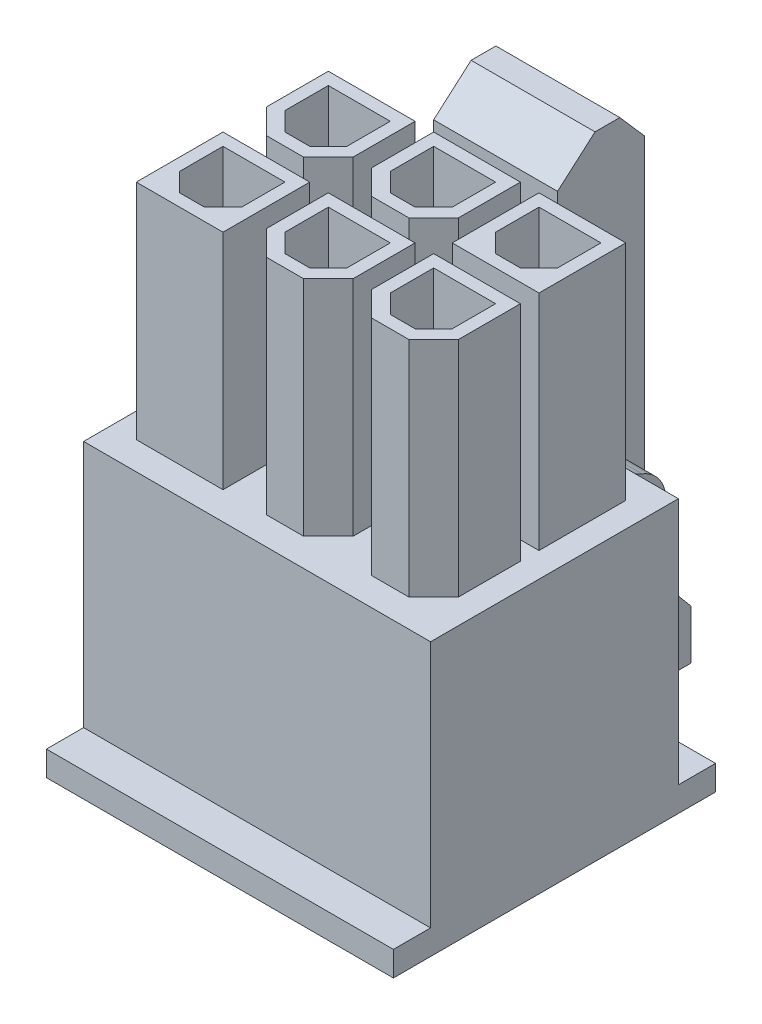
SolidWorks part; units mm, degrees
ref_plane "Ebene vorne" through (0, 0, 0) normal (0, 0, 1) x (1, 0, 0)
ref_plane "Ebene oben" through (0, 0, 0) normal (0, 1, 0) x (1, 0, 0)
ref_plane "Ebene rechts" through (0, 0, 0) normal (1, 0, 0) x (0, 0, -1)
sketch "Skizze1" plane through (0, 0, 0) normal (1, 0, 0) x (0, 0, -1)
  line L1 (5, 0) -> (-5, 0)
  line L2 (5, 0) -> (5, 11)
  line L3 (5, 11) -> (-5, 11)
  line L4 (-5, 0) -> (-5, 11)
  point P4 (0, 0)
  dimension "D1" = 10
  dimension "D2" = 11
extrude "Aufsatz-Linear austragen1" add sketch "Skizze1" along normal mid plane 14
sketch "Skizze2" plane through (0, 0, 0) normal (1, 0, 0) x (0, 0, -1)
  line L0 (0, 0) -> (0, 11) construction
  line L1 (-5, 0) -> (-6.5, 0)
  line L2 (-5, 0) -> (-5, 1)
  line L3 (-5, 1) -> (-6.5, 1)
  line L4 (-6.5, 0) -> (-6.5, 1)
  line L5 (5, 11) -> (-5, 11) construction
  line L6 (6.5, 0) -> (6.5, 1)
  line L7 (5, 1) -> (6.5, 1)
  line L8 (5, 0) -> (5, 1)
  line L9 (5, 0) -> (6.5, 0)
  dimension "D1" = 1.5
  dimension "D2" = 1
extrude "Aufsatz-Linear austragen2" add sketch "Skizze2" along normal mid plane 14
sketch "Skizze3" plane through (0, 0, 0) normal (1, 0, 0) x (0, 0, -1)
  line L0 (5, 11) -> (5.5717, 11)
  line L1 (7.5, 8.198) -> (7.5, 5.198)
  line L2 (7.5, 5.198) -> (8.5, 4)
  line L3 (8.5, 4) -> (8.5, 2)
  line L4 (8.5, 2) -> (6.5, 2)
  line L5 (6.5, 2) -> (6.5, 8)
  line L6 (6.5, 8) -> (5, 8)
  line L7 (5, 1) -> (5, 11) construction
  line L8 (5, 11) -> (5, 8)
  line L9 (-6.5, 0) -> (6.5, 0) construction
  arc A0 (5.5717, 11) -> (6.5359, 9.599) centre (7.0717, 11) ccw
  arc A1 (6.5359, 9.599) -> (7.5, 8.198) centre (6, 8.198) cw
  dimension "D5" = 1.5
  dimension "D1" = 2
  dimension "D2" = 1
  dimension "D3" = 2
  dimension "D4" = 2
  dimension "D6" = 3
  dimension "D7" = 1.5
  dimension "D8" = 3
extrude "Aufsatz-Linear austragen3" add sketch "Skizze3" along normal mid plane 8
sketch "Skizze4" plane through (0, 0, 0) normal (0, -1, 0) x (1, 0, 0)
  line L0 (7, -5) -> (-7, -5) construction
  line L1 (-2.5, -5) -> (2.5, -5)
  line L2 (-2.5, -5) -> (-2.5, -6.5)
  line L3 (-2.5, -6.5) -> (2.5, -6.5)
  line L4 (2.5, -5) -> (2.5, -6.5)
  line L5 (7, -6.5) -> (-7, -6.5) construction
  line L6 (0, -5) -> (0, 0) construction
  line L7 (-4, -6.5) -> (-4, -8.5) construction
  dimension "D1" = 1.5
extrude "Schnitt-Linear austragen1" cut sketch "Skizze4" against normal through all
sketch "Skizze5" plane through (0, 0, 0) normal (1, 0, 0) x (0, 0, -1)
  line L0 (8.1235, 4.451) -> (8.1235, 19.8707)
  line L1 (8.5, 4) -> (7.5, 5.198) construction
  line L2 (8.1235, 19.8707) -> (7.1363, 21)
  line L3 (7.1363, 21) -> (6.1363, 21)
  line L4 (6.1363, 21) -> (4.6235, 19.6776)
  line L5 (4.6235, 19.6776) -> (4.6235, 17.6776)
  line L6 (4.6235, 17.6776) -> (6.1235, 17.6776)
  line L7 (6.1235, 17.6776) -> (6.5, 8)
  line L8 (6.5, 8) -> (6.5, 2)
  line L9 (6.5, 2) -> (8.1235, 4.451)
  line L10 (5, 11) -> (-5, 11) construction
  dimension "D1" = 3.5
  dimension "D2" = 1.5
  dimension "D3" = 1
  dimension "D4" = 10
  dimension "D5" = 2
  dimension "D6" = 2.0093
  dimension "D7" = 1.5
extrude "Aufsatz-Linear austragen4" add sketch "Skizze5" along normal mid plane 5
sketch "Skizze6" plane through (0, 0, 0) normal (0, -1, 0) x (1, 0, 0)
  line L0 (-7, 6.5) -> (-7, -6.5) construction
  line L1 (-6.125, -4) -> (-2.375, -4)
  line L2 (-6.125, -4) -> (-6.125, -0.25)
  line L3 (-6.125, -0.25) -> (-2.375, -0.25)
  line L4 (-2.375, -4) -> (-2.375, -0.25)
  line L5 (-2.5, -5) -> (-7, -5) construction
  dimension "D1" = 0.875
  dimension "D2" = 1
  dimension "D3" = 3.75
extrude "Schnitt-Linear austragen2" cut sketch "Skizze6" against normal blind 10
pattern_linear "Lineares Muster1" count 3 spacing 4.25 along (1, 0, 0) count 2 spacing 4.25 along (0, 0, 1) of "Schnitt-Linear austragen2"
sketch "Skizze7" plane through (0, 11, 0) normal (0, 1, 0) x (1, 0, 0)
  line L1 (-2.375, -0.25) -> (-6.125, -4) construction
  line L2 (-6.125, -0.25) -> (-2.375, -4) construction
  line L4 (-6, -0.375) -> (-2.5, -0.375)
  line L6 (-6, -0.375) -> (-6, -3.875)
  line L8 (-6, -3.875) -> (-2.5, -3.875)
  line L10 (-2.5, -0.375) -> (-2.5, -3.875)
  line L11 (-6, -0.375) -> (-2.5, -3.875) construction
  point P4 (-4.25, -2.125)
  dimension "D1" = 3.5
extrude "Aufsatz-Linear austragen5" add sketch "Skizze7" along normal blind 9
pattern_linear "Lineares Muster2" count 3 spacing 4.25 along (1, 0, 0) count 2 spacing 4.25 along (0, 0, 1) of "Aufsatz-Linear austragen5"
sketch "Skizze10" plane through (0, 11, 0) normal (0, 1, 0) x (1, 0, 0)
  line L0 (-6.125, 4) -> (-2.375, 0.25) construction
  line L1 (-2.375, 4) -> (-6.125, 0.25) construction
  line L3 (-2.5, 1.375) -> (-3.5, 0.375)
  line L5 (-3.5, 0.375) -> (-5, 0.375)
  line L6 (-2.5, 1.375) -> (-2.5, 3.875)
  line L7 (-2.5, 3.875) -> (-6, 3.875)
  line L8 (-6, 1.375) -> (-6, 3.875)
  line L9 (-2.5, 0.375) -> (-6, 3.875) construction
  line L10 (-2.5, 3.875) -> (-6, 0.375) construction
  line L11 (-5, 0.375) -> (-6, 1.375)
  point P4 (-4.25, 2.125)
  dimension "D1" = 3.5
extrude "Aufsatz-Linear austragen7" add sketch "Skizze10" along normal up to surface (9 mm away) up to face at (-4.25, 20, 2.125)
pattern_linear "Lineares Muster4" count 3 spacing 4.25 along (1, 0, 0) count 2 spacing 4.25 along (0, 0, 1) skipping (0, 1), (2, 0) of "Aufsatz-Linear austragen7"
sketch "Skizze12" plane through (0, 20, 0) normal (0, 1, 0) x (1, 0, 0)
  line L16 (-6.125, 2.125) -> (-2.375, 2.125) construction
  line L17 (-4.25, 4) -> (-4.25, 0.25) construction
  line L18 (-6.125, 4) -> (-2.0043, -0.1207) construction
  line L19 (-3.75, 0.875) -> (-3, 1.625)
  line L20 (-5.5, 3.375) -> (-3, 3.375)
  line L21 (-5.5, 3.375) -> (-5.5, 1.625)
  line L22 (-4.75, 0.875) -> (-3.75, 0.875)
  line L23 (-3, 3.375) -> (-3, 1.625)
  line L24 (-5.5, 3.375) -> (-3, 0.875) construction
  line L25 (-5.5, 0.875) -> (-3, 3.375) construction
  line L26 (-5.5, 1.625) -> (-4.75, 0.875)
  line L27 (-2.375, 4) -> (-2.375, 0.25) construction
  line L28 (-6.125, 0.25) -> (-6.125, 4) construction
  line L29 (-6.125, 4) -> (-2.375, 4) construction
  line L30 (-2.375, 0.25) -> (-6.125, 0.25) construction
  point P35 (-4.25, 2.125)
  dimension "D1" = 2.5
  dimension "D3" = 0.75
  dimension "D4" = 0.75
  dimension "D5" = 0.75
  dimension "D6" = 0.75
  dimension "D7" = 2.5
extrude "Schnitt-Linear austragen4" cut sketch "Skizze12" against normal through all
pattern_linear "Lineares Muster6" count 3 spacing 4.25 along (1, 0, 0) count 2 spacing 4.25 along (0, 0, 1) of "Schnitt-Linear austragen4"
